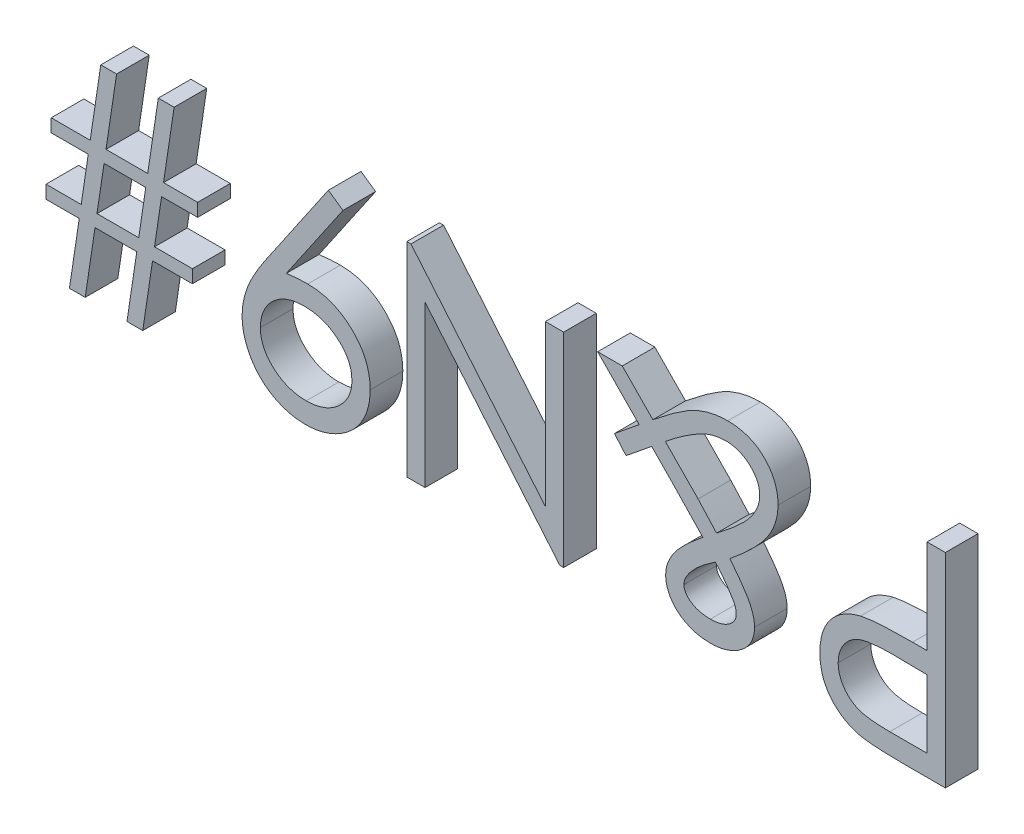
SolidWorks part; units mm, degrees
ref_plane "Front Plane" through (0, 0, 0) normal (0, 0, 1) x (1, 0, 0)
ref_plane "Top Plane" through (0, 0, 0) normal (0, 1, 0) x (1, 0, 0)
ref_plane "Right Plane" through (0, 0, 0) normal (1, 0, 0) x (0, 0, -1)
sketch "Sketch1" plane through (0, 0, 0) normal (0, 0, 1) x (1, 0, 0)
  line L0 (35.56, 0) -> (-35.56, 0) construction
  text T0 "P&N9#" font "Century Gothic" height in points 60
  point P4 (0, 0)
  dimension "D1" = 71.12
extrude "Boss-Extrude1" add sketch "Sketch1" along normal blind 2.54
